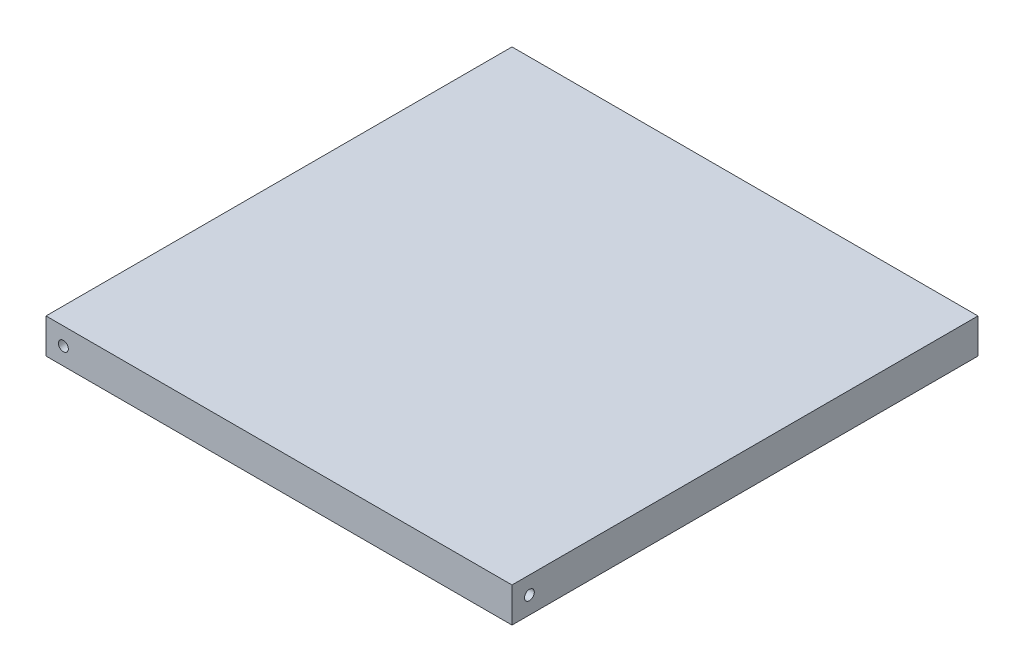
SolidWorks part; units mm, degrees
ref_plane "Front Plane" through (0, 0, 0) normal (0, 0, 1) x (1, 0, 0)
ref_plane "Top Plane" through (0, 0, 0) normal (0, 1, 0) x (1, 0, 0)
ref_plane "Right Plane" through (0, 0, 0) normal (1, 0, 0) x (0, 0, -1)
sketch "Sketch1" plane through (0, 0, 0) normal (0, 1, 0) x (1, 0, 0)
  line L1 (-63.8175, -63.8175) -> (63.8175, -63.8175)
  line L2 (-63.8175, -63.8175) -> (-63.8175, 63.8175)
  line L3 (-63.8175, 63.8175) -> (63.8175, 63.8175)
  line L4 (63.8175, -63.8175) -> (63.8175, 63.8175)
  line L5 (-63.8175, -63.8175) -> (63.8175, 63.8175) construction
  line L6 (-63.8175, 63.8175) -> (63.8175, -63.8175) construction
  point P0 (0, 0)
  dimension "D1" = 127.635
  dimension "D2" = 127.635
extrude "Boss-Extrude1" add sketch "Sketch1" along normal blind 9.525
sketch "Sketch2" plane through (0, 0, 63.8175) normal (0, 0, 1) x (1, 0, 0)
  line L0 (-63.8175, 0) -> (63.8175, 0) construction
  line L1 (-63.8175, 9.525) -> (-63.8175, 0) construction
  circle A0 centre (-59.055, 4.7625) radius 1.397
  dimension "D3" = 2.794
  dimension "D1" = 4.7625
  dimension "D2" = 4.7625
hole_wizard "Tap Drill for #6-32 Tap1" positions "Sketch6" profile "Sketch8" hole size "#6-32" standard "ANSI Inch"
sketch "Sketch6" plane through (0, 0, 63.8175) normal (0, 0, 1) x (1, 0, 0)
  point P0 (-59.055, 4.7625)
sketch "Sketch8" plane through (-59.055, 4.7625, 63.8175) normal (1, 0, 0) x (0, -1, 0)
  line L0 (0, 0) -> (0, 13.5127)
  line L1 (0, 13.5127) -> (1.3525, 12.7)
  line L2 (1.3525, 12.7) -> (1.3525, 0)
  line L5 (1.3525, 0) -> (0, 0)
  line L10 (0, 13.5127) -> (-1.3525, 12.7) construction
  line L11 (0, -6.35) -> (0, 107.95) construction
  dimension "Hole Dia." = 2.7051
  dimension "Hole Depth" = 12.7
  dimension "Drill Angle" = 118
pattern_circular "CirPattern1" count 4 over 360 about axis through (0, 9.525, 0) along (0, -1, 0) of "Tap Drill for #6-32 Tap1"
